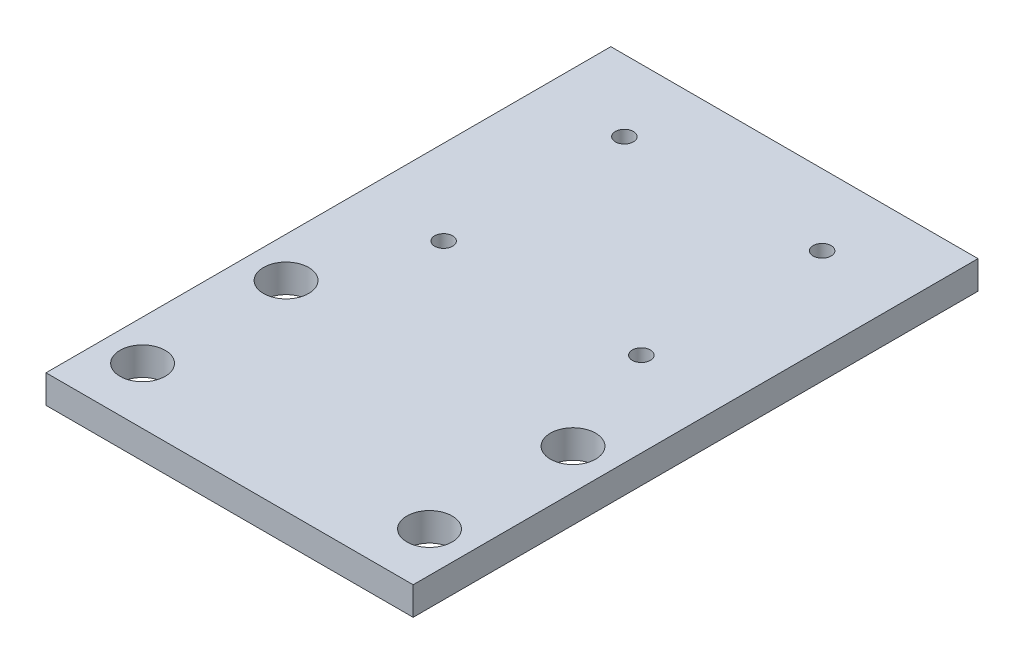
SolidWorks part; units mm, degrees
ref_plane "Front Plane" through (0, 0, 0) normal (0, 0, 1) x (1, 0, 0)
ref_plane "Top Plane" through (0, 0, 0) normal (0, 1, 0) x (1, 0, 0)
ref_plane "Right Plane" through (0, 0, 0) normal (1, 0, 0) x (0, 0, -1)
sketch "Sketch1" plane through (0, 0, 0) normal (0, 1, 0) x (1, 0, 0)
  line L0 (-25.4, -40) -> (25.4, -40) construction
  line L1 (-32.5, 50) -> (32.5, 50)
  line L2 (-32.5, 50) -> (-32.5, -50)
  line L3 (-32.5, -50) -> (32.5, -50)
  line L4 (32.5, 50) -> (32.5, -50)
  line L5 (-32.5, 50) -> (32.5, -50) construction
  line L6 (-32.5, -50) -> (32.5, 50) construction
  line L7 (0, -3.2164) -> (0, 21.8607) construction
  circle A0 centre (-25.4, -40) radius 4
  circle A1 centre (25.4, -40) radius 4
  circle A2 centre (25.4, -14.6) radius 4
  circle A3 centre (-25.4, -14.6) radius 4
  circle A4 centre (-17.5, 5.4) radius 1.6
  circle A5 centre (17.5, 37.4) radius 1.6
  circle A6 centre (-17.5, 37.4) radius 1.6
  circle A7 centre (17.5, 5.4) radius 1.6
  point P0 (0, 0)
  dimension "D3" = 8
  dimension "D4" = 8
  dimension "D8" = 3.2
  dimension "D9" = 3.2
  dimension "D1" = 65
  dimension "D2" = 100
  dimension "D5" = 50.8
  dimension "D6" = 10
  dimension "D7" = 2
  dimension "D10" = 35
  dimension "D11" = 32
  dimension "D12" = 0
  dimension "D13" = 20
extrude "Boss-Extrude1" add sketch "Sketch1" along normal blind 5
sketch "Sketch3" plane through (0, 0, 0) normal (0, -1, 0) x (1, 0, 0)
  circle A0 centre (-17.5, -5.4) radius 3.5
  circle A1 centre (17.5, -5.4) radius 3.5
  circle A2 centre (-17.5, -37.4) radius 3.5
  circle A3 centre (17.5, -37.4) radius 3.5
  dimension "D1" = 7
  dimension "D2" = 7
  dimension "D3" = 7
  dimension "D4" = 7
extrude "Cut-Extrude1" cut sketch "Sketch3" against normal blind 2
